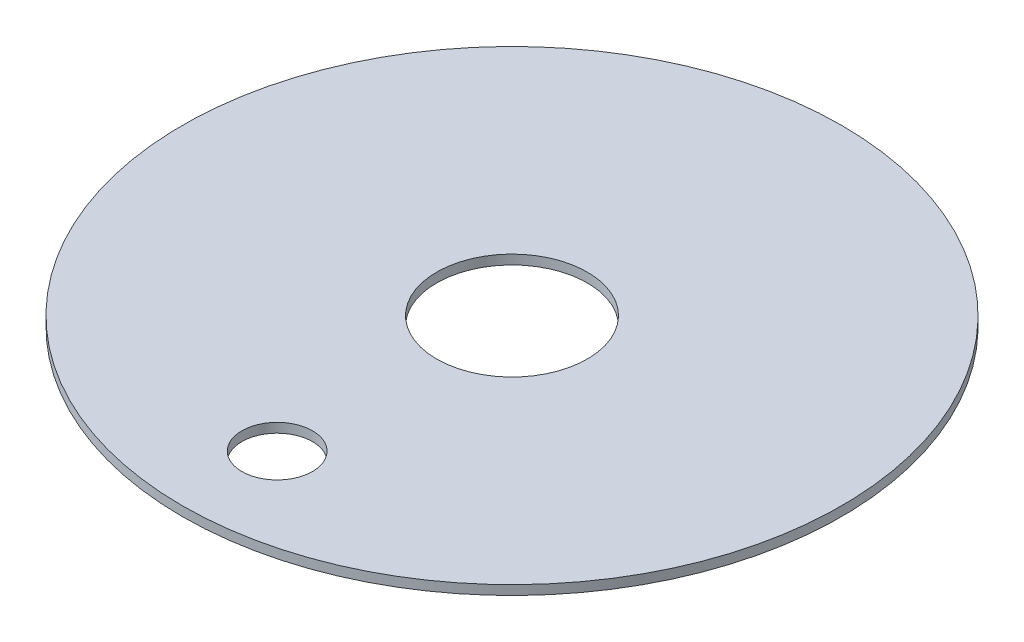
SolidWorks part; units mm, degrees
ref_plane "Front Plane" through (0, 0, 0) normal (0, 0, 1) x (1, 0, 0)
ref_plane "Top Plane" through (0, 0, 0) normal (0, 1, 0) x (1, 0, 0)
ref_plane "Right Plane" through (0, 0, 0) normal (1, 0, 0) x (0, 0, -1)
sketch "Sketch1" plane through (0, 0, 0) normal (0, 1, 0) x (1, 0, 0)
  circle A0 centre (0, 0) radius 70
  dimension "D1" = 140
extrude "Boss-Extrude1" add sketch "Sketch1" along normal blind 2
sketch "Sketch5" plane through (0, 2, 0) normal (0, 1, 0) x (1, 0, 0)
  circle A0 centre (0, 0) radius 16
  dimension "D1" = 32
extrude "Cut-Extrude2" cut sketch "Sketch5" against normal up to next
sketch "Sketch6" plane through (0, 2, 0) normal (0, 1, 0) x (1, 0, 0)
  line L1 (0, 0) -> (0, -70) construction
  circle A0 centre (0, -49.88) radius 7.5
  circle A1 centre (0, 0) radius 16 construction
  circle A2 centre (0, 0) radius 70 construction
  dimension "D1" = 49.88
  dimension "D2" = 15
extrude "Cut-Extrude3" cut sketch "Sketch6" against normal blind 10
sketch "Sketch7" plane through (0, 0, 0) normal (0, 1, 0) x (1, 0, 0)
  circle A0 centre (0, -60.88) radius 1
  circle A1 centre (0, -49.88) radius 7.5 construction
  dimension "D1" = 2
  dimension "D2" = 11
extrude "Boss-Extrude2" add sketch "Sketch7" against normal blind 4
fillet "Fillet1" radius 1 1 edges at (0, -4, 61.88)
